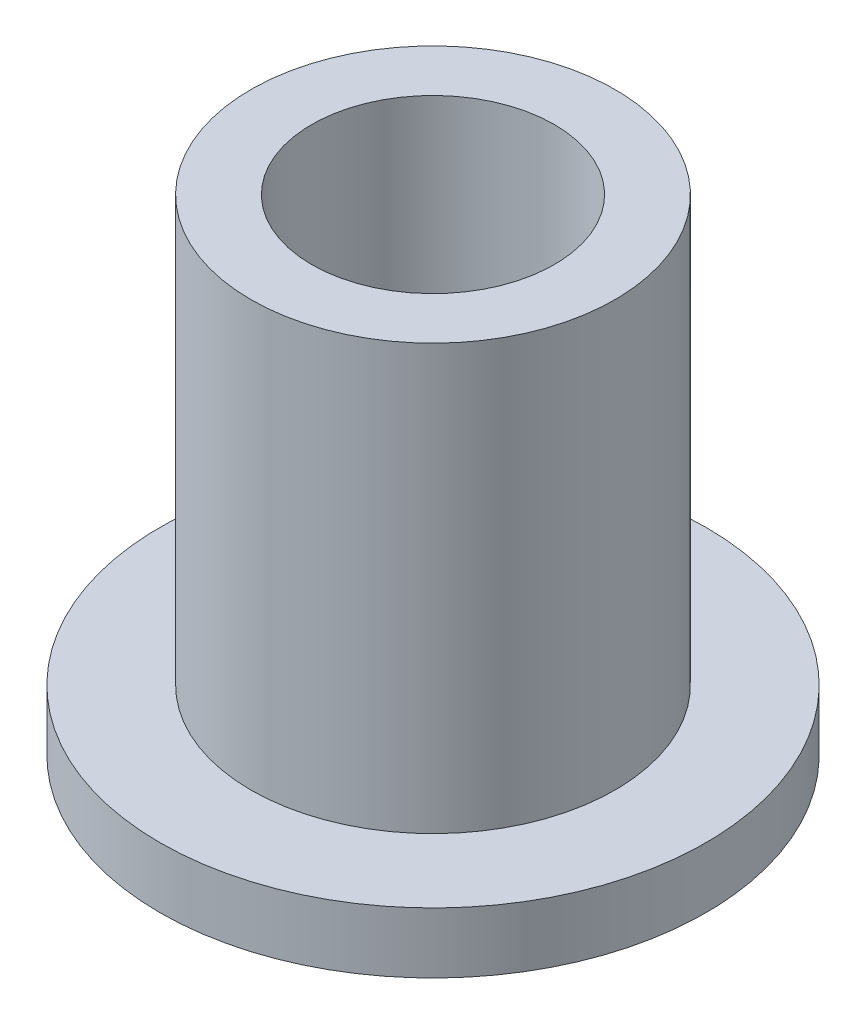
SolidWorks part; units mm, degrees
ref_plane "Front" through (0, 0, 0) normal (0, 0, 1) x (1, 0, 0)
ref_plane "Top" through (0, 0, 0) normal (0, 1, 0) x (1, 0, 0)
ref_plane "Right" through (0, 0, 0) normal (1, 0, 0) x (0, 0, -1)
sketch "Sketch1" plane through (0, 0, 0) normal (0, 1, 0) x (1, 0, 0)
  circle A0 centre (0, 0) radius 3.175
  circle A1 centre (0, 0) radius 4.7625
  circle A2 centre (0, 0) radius 7.1438
  dimension "ID" = 6.35
  dimension "OD" = 9.525
  dimension "FlangeOD" = 14.2875
sketch "Sketch2" plane through (0, 0, 0) normal (0, 1, 0) x (1, 0, 0)
  circle A0 centre (0, 0) radius 3.175 construction
  circle A1 centre (0, 0) radius 4.7625 construction
  circle A2 centre (0, 0) radius 3.175
  circle A3 centre (0, 0) radius 4.7625
extrude "Boss-Extrude1" add sketch "Sketch2" along normal blind 12.7
sketch "Sketch3" plane through (0, 0, 0) normal (0, 1, 0) x (1, 0, 0)
  circle A0 centre (0, 0) radius 7.1438 construction
  circle A1 centre (0, 0) radius 4.7625 construction
  circle A2 centre (0, 0) radius 7.1438
  circle A3 centre (0, 0) radius 4.7625
extrude "Boss-Extrude2" add sketch "Sketch3" along normal blind 1.5875
